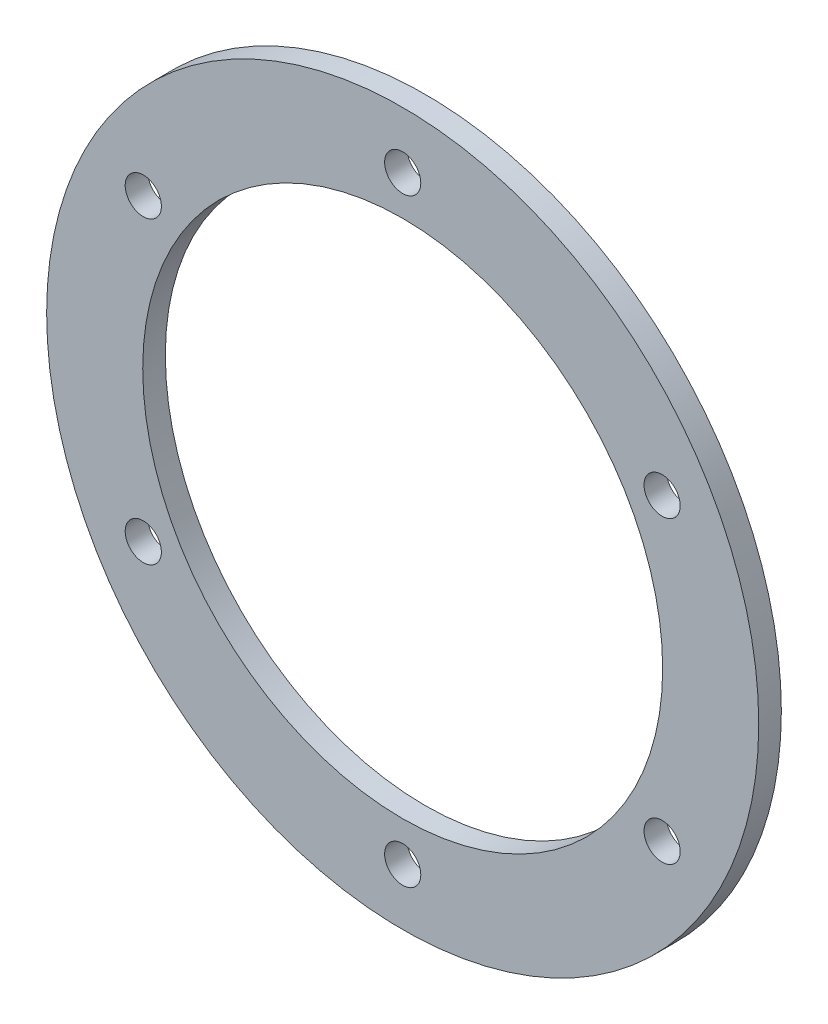
SolidWorks part; units mm, degrees
material "A-玻璃纤维"
ref_plane "前视基准面" through (0, 0, 0) normal (0, 0, 1) x (1, 0, 0)
ref_plane "上视基准面" through (0, 0, 0) normal (0, 1, 0) x (1, 0, 0)
ref_plane "右视基准面" through (0, 0, 0) normal (1, 0, 0) x (0, 0, -1)
sketch "草图1" plane through (0, 0, 0) normal (0, 0, 1) x (1, 0, 0)
  circle A0 centre (0, 0) radius 23
  circle A1 centre (0, 0) radius 31.5
  circle A2 centre (0, 0) radius 26.5 construction
  circle A3 centre (0, 26.5) radius 1.6
  circle A4 centre (22.9497, 13.25) radius 1.6
  circle A5 centre (22.9497, -13.25) radius 1.6
  circle A6 centre (0, -26.5) radius 1.6
  circle A7 centre (-22.9497, -13.25) radius 1.6
  circle A8 centre (-22.9497, 13.25) radius 1.6
  point P19 (0, 0)
  dimension "D1" = 63
  dimension "D2" = 46
  dimension "D3" = 53
  dimension "D4" = 3.2
  dimension "D5" = 6
extrude "凸台-拉伸1" add sketch "草图1" along normal blind 2
